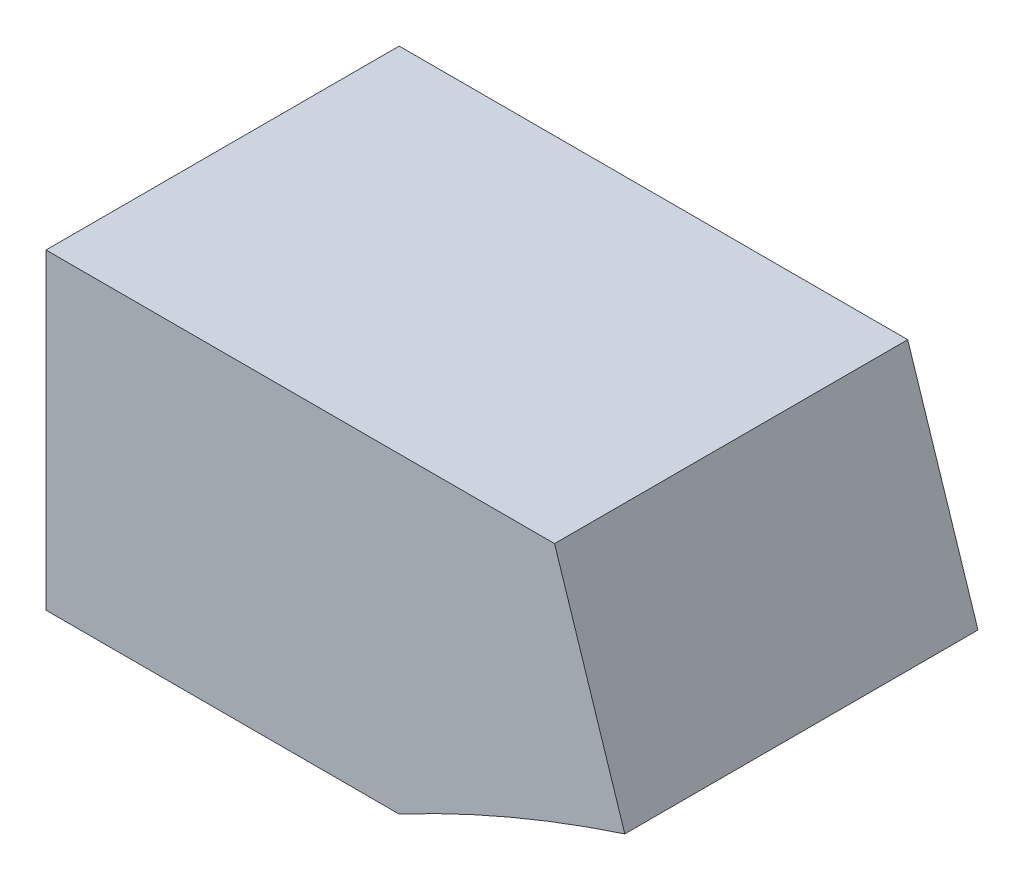
SolidWorks part; units mm, degrees
material "砖"
ref_plane "前视基准面" through (0, 0, 0) normal (0, 0, 1) x (1, 0, 0)
ref_plane "上视基准面" through (0, 0, 0) normal (0, 1, 0) x (1, 0, 0)
ref_plane "右视基准面" through (0, 0, 0) normal (1, 0, 0) x (0, 0, -1)
sketch "草图1" plane through (0, 0, 0) normal (0, 0, 1) x (1, 0, 0)
  line L0 (-4560, 0) -> (-7920, 0)
  line L1 (-12480, 7680) -> (0, 7680)
  line L2 (-12480, 7680) -> (-12480, 0)
  line L3 (-12480, 0) -> (0, 0)
  line L4 (0, 7680) -> (0, 0)
  line L5 (-7920, 0) -> (-7920, 3840)
  line L6 (-7920, 3840) -> (-4560, 3840)
  line L7 (-4560, 3840) -> (-4560, 0)
  line L8 (-7920, 3840) -> (-8160, 3840)
  line L9 (-4560, 3840) -> (-4320, 3840)
  line L10 (-7837.7749, 4359.1486) -> (-8066.0285, 4433.3126)
  line L11 (-7599.1486, 4827.4792) -> (-7793.3126, 4968.5477)
  line L12 (-7227.4792, 5199.1486) -> (-7368.5477, 5393.3126)
  line L13 (-6759.1486, 5437.7749) -> (-6833.3126, 5666.0285)
  line L14 (-6240, 5520) -> (-6240, 5760)
  line L15 (-5720.8514, 5437.7749) -> (-5646.6874, 5666.0285)
  line L16 (-5252.5208, 5199.1486) -> (-5111.4523, 5393.3126)
  line L17 (-4880.8514, 4827.4792) -> (-4686.6874, 4968.5477)
  line L18 (-4642.2251, 4359.1486) -> (-4413.9715, 4433.3126)
  line L19 (-4560, 3840) -> (-4320, 3840)
  line L20 (-4573.7633, 3298.6069) -> (-4560, 3294.1349)
  line L21 (-6833.3126, 5666.0285) -> (-6928.8298, 5960)
  line L22 (-5683.7694, 5551.9017) -> (-5551.1702, 5960)
  line L23 (-5551.1702, 5960) -> (-6928.8298, 5960)
  line L24 (-7920, 0) -> (-9123.3069, 0)
  line L25 (-8160, 0) -> (-8640, 0)
  line L26 (-8160, 0) -> (-8640, 0)
  line L27 (-8640, 3840) -> (-8160, 3840)
  line L28 (-8640, 3840) -> (-8640, 4264)
  line L29 (-7837.7749, 3320.8514) -> (-7920, 3294.1349) [skipped]
  line L30 (-7599.1486, 2852.5208) -> (-7793.3126, 2711.4523) [skipped]
  line L31 (-7227.4792, 2480.8514) -> (-7368.5477, 2286.6874) [skipped]
  line L32 (-6759.1486, 2242.2251) -> (-6833.3126, 2013.9715) [skipped]
  line L33 (-6240, 2160) -> (-6240, 1920) [skipped]
  line L34 (-5720.8514, 2242.2251) -> (-5646.6874, 2013.9715) [skipped]
  line L35 (-5252.5208, 2480.8514) -> (-5111.4523, 2286.6874) [skipped]
  line L36 (-4880.8514, 2852.5208) -> (-4686.6874, 2711.4523) [skipped]
  line L37 (-8640, 4264) -> (-8112.5982, 4264)
  line L38 (-8112.5982, 4264) -> (-8592.5982, 4264)
  line L39 (-8592.5982, 4264) -> (-8592.5982, 4688)
  line L40 (-8592.5982, 4688) -> (-7962.5841, 4688)
  line L41 (-7962.5841, 4688) -> (-8442.5841, 4688)
  line L42 (-8442.5841, 4688) -> (-8442.5841, 5112)
  line L43 (-8442.5841, 5112) -> (-7678.1989, 5112)
  line L44 (-7678.1989, 5112) -> (-8158.1989, 5112)
  line L45 (-8158.1989, 5112) -> (-8158.1989, 5536)
  line L46 (-8158.1989, 5536) -> (-7139.9911, 5536)
  line L47 (-7139.9911, 5536) -> (-7619.9911, 5536)
  line L48 (-7619.9911, 5536) -> (-7619.9911, 5960)
  line L49 (-7619.9911, 5960) -> (-6928.8298, 5960)
  arc A0 (-4560, 3840) -> (-7920, 3840) centre (-6240, 3840) ccw
  arc A1 (-4320, 3840) -> (-8160, 3840) centre (-6240, 3840) ccw
  point P7 (-6240, 0)
  point P56 (-6240, 3840)
  dimension "D5" = 3840
  dimension "D1" = 12480
  dimension "D2" = 7680
  dimension "D3" = 3360
  dimension "D4" = 3840
  dimension "D7" = 240
  dimension "D8" = 480
  dimension "D9" = 424
  dimension "D10" = 720
  dimension "D11" = 480
  dimension "D12" = 480
  dimension "D13" = 480
  dimension "D14" = 480
  dimension "D6" = 20
extrude "凸台-拉伸1" add sketch "草图1" along normal blind 480 contours A1 L21 L49 L48 L46
scale "缩放比例1" scale about origin uniform scaling yes scale factor 1.3
